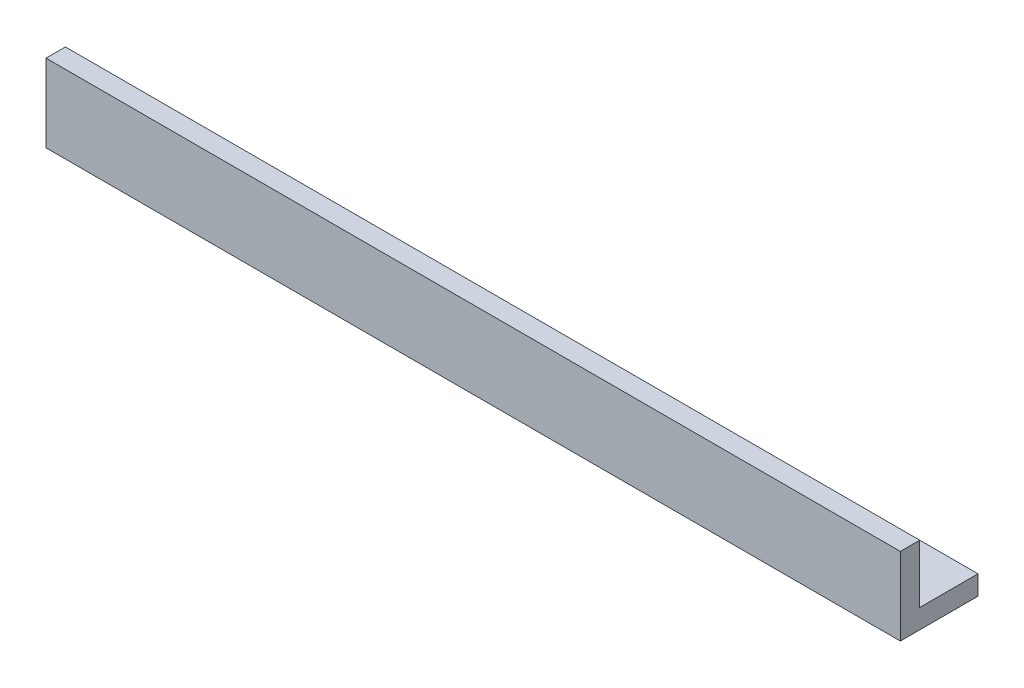
SolidWorks part; units mm, degrees
ref_plane "Front Plane" through (0, 0, 0) normal (0, 0, 1) x (1, 0, 0)
ref_plane "Top Plane" through (0, 0, 0) normal (0, 1, 0) x (1, 0, 0)
ref_plane "Right Plane" through (0, 0, 0) normal (1, 0, 0) x (0, 0, -1)
sketch "Sketch1" plane through (0, 0, 0) normal (0, 0, 1) x (1, 0, 0)
  line L1 (-67.9135, 28.7043) -> (71.7865, 28.7043)
  line L2 (-67.9135, 28.7043) -> (-67.9135, 16.0043)
  line L3 (-67.9135, 16.0043) -> (71.7865, 16.0043)
  line L4 (71.7865, 28.7043) -> (71.7865, 16.0043)
  dimension "D1" = 139.7
  dimension "D2" = 12.7
extrude "Boss-Extrude1" add sketch "Sketch1" along normal blind 3.175
ref_plane "Plane1" through (71.7865, 16.0043, 3.175) normal (1, 0, 0) x (0, 0, -1)
ref_plane "Plane2" through (-67.9135, 28.7043, 3.175) normal (0, 0, -1) x (-1, 0, 0)
ref_plane "Plane3" through (-67.9135, 16.0043, 3.175) normal (1, 0, 0) x (0, 0, -1)
sketch "Sketch7" plane through (0, 16.0043, 0) normal (0, -1, 0) x (-1, 0, 0)
  line L0 (67.9135, 0) -> (-71.7865, 0) construction
  line L1 (67.9135, 9.525) -> (-71.7865, 9.525)
  line L2 (67.9135, 9.525) -> (67.9135, 0)
  line L3 (67.9135, 0) -> (-71.7865, 0)
  line L4 (-71.7865, 9.525) -> (-71.7865, 0)
  dimension "D1" = 139.7
  dimension "D2" = 9.525
  dimension "D3" = 0
  dimension "D4" = 0
extrude "Boss-Extrude2" add sketch "Sketch7" against normal blind 3.175
